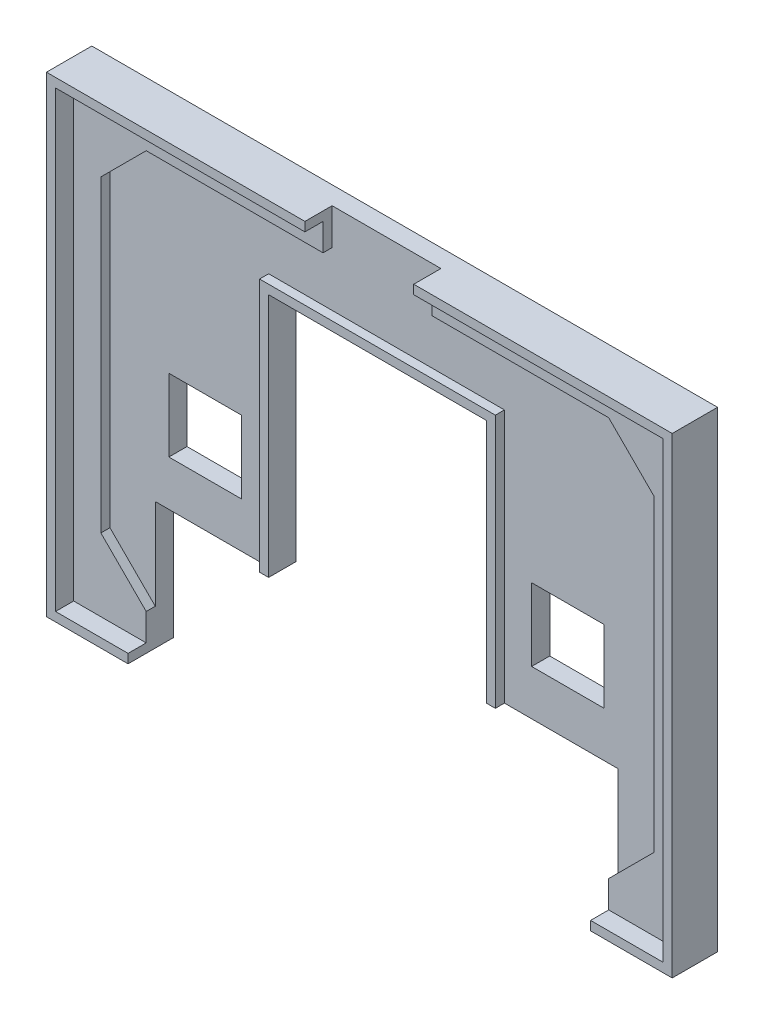
SolidWorks part; units mm, degrees
ref_plane "Přední rovina" through (0, 0, 0) normal (0, 0, 1) x (1, 0, 0)
ref_plane "Horní rovina" through (0, 0, 0) normal (0, 1, 0) x (1, 0, 0)
ref_plane "Pravá rovina" through (0, 0, 0) normal (1, 0, 0) x (0, 0, -1)
sketch "Skica1" plane through (0, 0, 0) normal (0, 0, 1) x (1, 0, 0)
  line L1 (-33.5, -25) -> (33.5, -25)
  line L2 (-33.5, -25) -> (-33.5, 25)
  line L3 (-33.5, 25) -> (33.5, 25)
  line L4 (33.5, -25) -> (33.5, 25)
  line L5 (-33.5, -25) -> (33.5, 25) construction
  line L6 (-33.5, 25) -> (33.5, -25) construction
  point P0 (0, 0)
  dimension "D1" = 67
  dimension "D2" = 50
extrude "Přidat vysunutím1" add sketch "Skica1" along normal blind 3
sketch "Skica2" plane through (0, 0, 3) normal (0, 0, 1) x (1, 0, 0)
  line L0 (-1000, 0) -> (49000, 0) construction
  line L1 (0, -1000) -> (0, 49000) construction
  line L2 (-1000, -22) -> (49000, -22) construction
  line L3 (-25.5, -1000) -> (-25.5, 49000) construction
  line L4 (-30.5, -1000) -> (-30.5, 49000) construction
  line L6 (-33.5, -25) -> (33.5, -25) construction
  line L7 (-25.5, -22) -> (-30.5, -17)
  line L8 (-30.5, -17) -> (-30.5, 17)
  line L9 (-25.5, -22) -> (25.5, -22)
  line L10 (30.5, -17) -> (30.5, 17)
  line L11 (25.5, -22) -> (30.5, -17)
  line L12 (25.5, 22) -> (30.5, 17)
  line L13 (-25.5, 22) -> (25.5, 22)
  line L14 (-25.5, 22) -> (-30.5, 17)
  point P20 (0, -22)
  point P21 (30.5, 0)
  point P24 (-30.5, 0)
  dimension "D1" = 30.5
  dimension "D2" = 5
  dimension "D3" = 3
  dimension "D4" = 45
extrude "Odebrat vysunutím1" cut sketch "Skica2" against normal offset from surface (1 mm away) 2 up to face at (0, 0, 0)
sketch "Skica3" plane through (0, 0, 0) normal (0, 0, -1) x (-1, 0, 0)
  line L0 (0, -1000) -> (0, 49000) construction
  line L1 (33.5, -25) -> (-33.5, -25) construction
  line L2 (24, 1) -> (16, 1)
  line L3 (24, 1) -> (24, -7)
  line L4 (24, -7) -> (16, -7)
  line L5 (16, 1) -> (16, -7)
  line L6 (-16, 1) -> (-16, -7)
  line L7 (33.5, -25) -> (-33.5, -25) construction
  line L8 (25.5, -25) -> (-25.5, -25)
  line L9 (25.5, -25) -> (25.5, -12)
  line L11 (-25.5, -25) -> (-25.5, -12)
  line L12 (-24, -7) -> (-16, -7)
  line L13 (25.5, -12) -> (12, -12)
  line L15 (12, -12) -> (12, 15)
  line L16 (12, 15) -> (-12, 15)
  line L17 (-12, -12) -> (-12, 15)
  line L18 (-12, -12) -> (-25.5, -12)
  line L19 (-24, 1) -> (-24, -7)
  line L20 (-24, 1) -> (-16, 1)
  dimension "D1" = 16
  dimension "D2" = 8
  dimension "D3" = 18
  dimension "D4" = 13
  dimension "D5" = 51
  dimension "D6" = 24
  dimension "D7" = 27
extrude "Odebrat vysunutím2" cut sketch "Skica3" against normal through all
sketch "Skica4" plane through (0, 0, 2) normal (0, 0, 1) x (1, 0, 0)
  line L0 (12, 15) -> (12, -12) construction
  line L1 (-12, -12) -> (-12, 15) construction
  line L2 (-12, 15) -> (12, 15) construction
  line L3 (12, 15) -> (12, -12)
  line L4 (-12, -12) -> (-12, 15)
  line L5 (-12, 15) -> (12, 15)
extrude "Vysunout tenkostěnný1" add sketch "Skica4" along normal up to surface (1 mm away) thin up to face at (0, -3.5714, 3) thin type one direction reverse wall 1
sketch "Skica5" plane through (0, 0, 0) normal (0, 0, -1) x (-1, 0, 0)
  line L0 (-33.5, 25) -> (33.5, 25) construction
  line L1 (33.5, 25) -> (33.5, -25) construction
  line L2 (33.5, -25) -> (25.5, -25) construction
  line L3 (-33.5, -25) -> (-33.5, 25) construction
  line L4 (-25.5, -25) -> (-33.5, -25) construction
  line L5 (-33.5, 25) -> (33.5, 25)
  line L6 (33.5, 25) -> (33.5, -25)
  line L7 (33.5, -25) -> (25.5, -25)
  line L8 (-33.5, -25) -> (-33.5, 25)
  line L9 (-25.5, -25) -> (-33.5, -25)
extrude "Vysunout tenkostěnný2" add sketch "Skica5" against normal blind 5 thin thin type one direction reverse wall 1
sketch "Skica6" plane through (0, 0, 2) normal (0, 0, 1) x (1, 0, 0)
  line L0 (0, -1000) -> (0, 49000) construction
  line L1 (25.5, 22) -> (-25.5, 22) construction
  line L2 (-6, 22) -> (6, 22)
  line L3 (-6, 22) -> (-6, 26)
  line L4 (-6, 26) -> (6, 26)
  line L5 (6, 22) -> (6, 26)
  line L6 (34.5, 26) -> (-34.5, 26) construction
  dimension "D1" = 12
extrude "Odebrat vysunutím3" cut sketch "Skica6" along normal through all
sketch "Skica8" plane through (0, 0, 0) normal (0, 0, -1) x (-1, 0, 0)
  line L0 (-30.2787, 21.3288) -> (-28.1098, 21.3288)
  line L1 (-28.1098, 21.3288) -> (-28.1098, 20.2286)
  line L2 (-28.1098, 20.2286) -> (-27.0096, 20.2286)
  line L3 (-27.0096, 20.2286) -> (-27.0096, 17.9968)
  line L4 (-27.0096, 17.9968) -> (-19.371, 17.9968)
  line L5 (-19.371, 17.9968) -> (-19.371, 20.2286)
  line L6 (-19.371, 20.2286) -> (-18.3022, 20.2286)
  line L7 (-18.3022, 20.2286) -> (-18.3022, 21.3288)
  line L8 (-18.3022, 21.3288) -> (-15.9447, 21.3288)
  line L9 (-15.9447, 21.3288) -> (-15.9447, 20.2286)
  line L10 (-15.9447, 20.2286) -> (-14.8445, 20.2286)
  line L12 (-14.8445, 8.9437) -> (-15.9447, 8.9437)
  line L13 (-15.9447, 8.9437) -> (-15.9447, 7.9692)
  line L14 (-15.9447, 7.9692) -> (-17.1234, 7.9692)
  line L15 (-17.1234, 7.9692) -> (-17.1234, 6.8061)
  line L16 (-17.1234, 6.8061) -> (-18.3022, 6.8061)
  line L17 (-18.3022, 6.8061) -> (-18.3022, 5.7374)
  line L18 (-18.3022, 5.7374) -> (-28.1098, 5.7374)
  line L19 (-28.1098, 5.7374) -> (-28.1098, 6.8061)
  line L20 (-28.1098, 6.8061) -> (-29.1943, 6.8061)
  line L21 (-29.1943, 6.8061) -> (-29.1943, 7.9692)
  line L22 (-29.1943, 7.9692) -> (-30.2787, 7.9692)
  line L23 (-30.2787, 7.9692) -> (-30.2787, 8.9437)
  line L24 (-30.2787, 8.9437) -> (-31.4733, 8.9437)
  line L25 (-31.4733, 8.9437) -> (-31.4733, 15.7021)
  line L26 (-31.4733, 15.7021) -> (-30.2787, 15.7021)
  line L27 (-30.2787, 15.7021) -> (-30.2787, 16.8337)
  line L28 (-30.2787, 16.8337) -> (-31.4733, 16.8337)
  line L29 (-31.4733, 16.8337) -> (-31.4733, 20.2286)
  line L30 (-31.4733, 20.2286) -> (-30.2787, 20.2286)
  line L31 (-30.2787, 20.2286) -> (-30.2787, 21.3288)
  line L32 (-14.8445, 20.2286) -> (-14.8445, 16.8337)
  line L33 (-14.8445, 16.8337) -> (-15.9447, 16.8337)
  line L34 (-15.9447, 16.8337) -> (-15.9447, 15.7021)
  line L35 (-15.9447, 15.7021) -> (-14.8445, 15.7021)
  line L36 (-14.8445, 15.7021) -> (-14.8445, 8.9437)
  line L37 (0, 0) -> (0, 59.9257) construction
  line L38 (15.9447, 15.7021) -> (14.8445, 15.7021)
  line L39 (15.9447, 16.8337) -> (15.9447, 15.7021)
  line L40 (14.8445, 16.8337) -> (15.9447, 16.8337)
  line L41 (14.8445, 20.2286) -> (14.8445, 16.8337)
  line L42 (15.9447, 20.2286) -> (14.8445, 20.2286)
  line L43 (15.9447, 21.3288) -> (15.9447, 20.2286)
  line L44 (18.3022, 21.3288) -> (15.9447, 21.3288)
  line L45 (18.3022, 20.2286) -> (18.3022, 21.3288)
  line L46 (19.371, 20.2286) -> (18.3022, 20.2286)
  line L47 (19.371, 17.9968) -> (19.371, 20.2286)
  line L48 (27.0096, 17.9968) -> (19.371, 17.9968)
  line L49 (27.0096, 20.2286) -> (27.0096, 17.9968)
  line L50 (28.1098, 20.2286) -> (27.0096, 20.2286)
  line L51 (28.1098, 21.3288) -> (28.1098, 20.2286)
  line L52 (30.2787, 21.3288) -> (28.1098, 21.3288)
  line L53 (30.2787, 20.2286) -> (30.2787, 21.3288)
  line L54 (31.4733, 20.2286) -> (30.2787, 20.2286)
  line L55 (31.4733, 16.8337) -> (31.4733, 20.2286)
  line L56 (30.2787, 16.8337) -> (31.4733, 16.8337)
  line L57 (30.2787, 15.7021) -> (30.2787, 16.8337)
  line L58 (31.4733, 15.7021) -> (30.2787, 15.7021)
  line L59 (31.4733, 8.9437) -> (31.4733, 15.7021)
  line L60 (30.2787, 8.9437) -> (31.4733, 8.9437)
  line L61 (30.2787, 7.9692) -> (30.2787, 8.9437)
  line L62 (29.1943, 7.9692) -> (30.2787, 7.9692)
  line L63 (29.1943, 6.8061) -> (29.1943, 7.9692)
  line L64 (28.1098, 6.8061) -> (29.1943, 6.8061)
  line L65 (28.1098, 5.7374) -> (28.1098, 6.8061)
  line L66 (18.3022, 5.7374) -> (28.1098, 5.7374)
  line L67 (18.3022, 6.8061) -> (18.3022, 5.7374)
  line L68 (17.1234, 6.8061) -> (18.3022, 6.8061)
  line L69 (17.1234, 7.9692) -> (17.1234, 6.8061)
  line L70 (15.9447, 7.9692) -> (17.1234, 7.9692)
  line L71 (15.9447, 8.9437) -> (15.9447, 7.9692)
  line L72 (14.8445, 8.9437) -> (15.9447, 8.9437)
  line L73 (14.8445, 15.7021) -> (14.8445, 8.9437)
  line L74 (34.5, 26) -> (34.5, -26) construction
  line L75 (34.5, -26) -> (25.5, -26) construction
  dimension "D1" = 3.0267
  dimension "D2" = 4.2213
  dimension "D3" = 5.3057
  dimension "D4" = 7.4904
  dimension "D5" = 15.129
  dimension "D6" = 16.1978
  dimension "D7" = 17.3766
  dimension "D8" = 31.7374
  dimension "D9" = 33.9692
  dimension "D10" = 34.9437
  dimension "D11" = 41.7021
  dimension "D12" = 42.8337
  dimension "D13" = 43.9968
  dimension "D14" = 46.2286
extrude "Odebrat vysunutím4" cut sketch "Skica8" against normal blind 1
sketch "Skica9" plane through (0, 0, 0) normal (0, 0, -1) x (-1, 0, 0)
  line L0 (-23.1903, 17.9968) -> (-23.1903, 11.1513) construction
  line L1 (-27.9647, 14.7021) -> (-25.9647, 14.7021)
  line L2 (-27.9647, 14.7021) -> (-27.9647, 12.7021)
  line L3 (-27.9647, 12.7021) -> (-25.9647, 12.7021)
  line L4 (-25.9647, 14.7021) -> (-25.9647, 12.7021)
  line L5 (-19.371, 17.9968) -> (-27.0096, 17.9968) construction
  line L6 (-30.2787, 15.7021) -> (-31.4733, 15.7021) construction
  line L7 (-18.4158, 12.7021) -> (-20.4158, 12.7021)
  line L8 (-20.4158, 14.7021) -> (-20.4158, 12.7021)
  line L9 (-18.4158, 14.7021) -> (-20.4158, 14.7021)
  line L10 (-18.4158, 14.7021) -> (-18.4158, 12.7021)
  line L11 (-24.9876, 11.1513) -> (-21.393, 11.1513)
  line L12 (-23.8756, 7.3916) -> (-22.505, 7.3916)
  line L14 (-23.8756, 7.3916) -> (-23.8756, 10.1452)
  line L15 (-23.8756, 10.1452) -> (-24.9876, 10.1452)
  line L16 (-24.9876, 10.1452) -> (-24.9876, 11.1513)
  line L19 (-21.393, 10.1452) -> (-21.393, 11.1513)
  line L20 (-22.505, 10.1452) -> (-21.393, 10.1452)
  line L21 (-22.505, 7.3916) -> (-22.505, 10.1452)
  line L22 (0, 0) -> (0, 34.6324) construction
  line L23 (-31.4733, 15.7021) -> (-31.4733, 8.9437) construction
  line L24 (-28.1098, 5.7374) -> (-18.3022, 5.7374) construction
  line L25 (-15.9447, 7.9692) -> (-15.9447, 8.9437) construction
  line L26 (-28.1098, 5.7374) -> (-18.3022, 5.7374) construction
  line L27 (-14.8445, 8.9437) -> (-14.8445, 15.7021) construction
  line L28 (-14.8445, 8.9437) -> (-14.8445, 15.7021) construction
  line L29 (23.8756, 7.3916) -> (23.8756, 10.1452)
  line L30 (23.8756, 10.1452) -> (24.9876, 10.1452)
  line L31 (24.9876, 10.1452) -> (24.9876, 11.1513)
  line L32 (24.9876, 11.1513) -> (21.393, 11.1513)
  line L33 (21.393, 10.1452) -> (21.393, 11.1513)
  line L34 (22.505, 10.1452) -> (21.393, 10.1452)
  line L35 (22.505, 7.3916) -> (22.505, 10.1452)
  line L36 (23.8756, 7.3916) -> (22.505, 7.3916)
  line L37 (27.9647, 12.7021) -> (25.9647, 12.7021)
  line L38 (25.9647, 14.7021) -> (25.9647, 12.7021)
  line L39 (27.9647, 14.7021) -> (25.9647, 14.7021)
  line L40 (27.9647, 14.7021) -> (27.9647, 12.7021)
  line L41 (18.4158, 14.7021) -> (18.4158, 12.7021)
  line L42 (18.4158, 14.7021) -> (20.4158, 14.7021)
  line L43 (20.4158, 14.7021) -> (20.4158, 12.7021)
  line L44 (18.4158, 12.7021) -> (20.4158, 12.7021)
  dimension "D1" = 1
  dimension "D2" = 2
  dimension "D3" = 2
  dimension "D4" = 6.8455
  dimension "D5" = 6.5604
  dimension "D6" = 1.6542
  dimension "D7" = 6.5485
  dimension "D8" = 4.4078
  dimension "D9" = 3.5714
extrude "Přidat vysunutím3" add sketch "Skica9" along normal blind 1 from offset 1 offset against normal yes
sketch "Skica10" plane through (0, 0, 0) normal (0, 0, -1) x (-1, 0, 0)
  line L0 (-31.4733, 15.7021) -> (-31.4733, 8.9437) construction
  line L1 (-28.1098, 5.7374) -> (-18.3022, 5.7374) construction
  text T0 "TEDY" font "BLOXAT" height 6
  dimension "D1" = 20.4106
  dimension "D2" = 11.7235
extrude "Odebrat vysunutím5" cut sketch "Skica10" against normal blind 1
